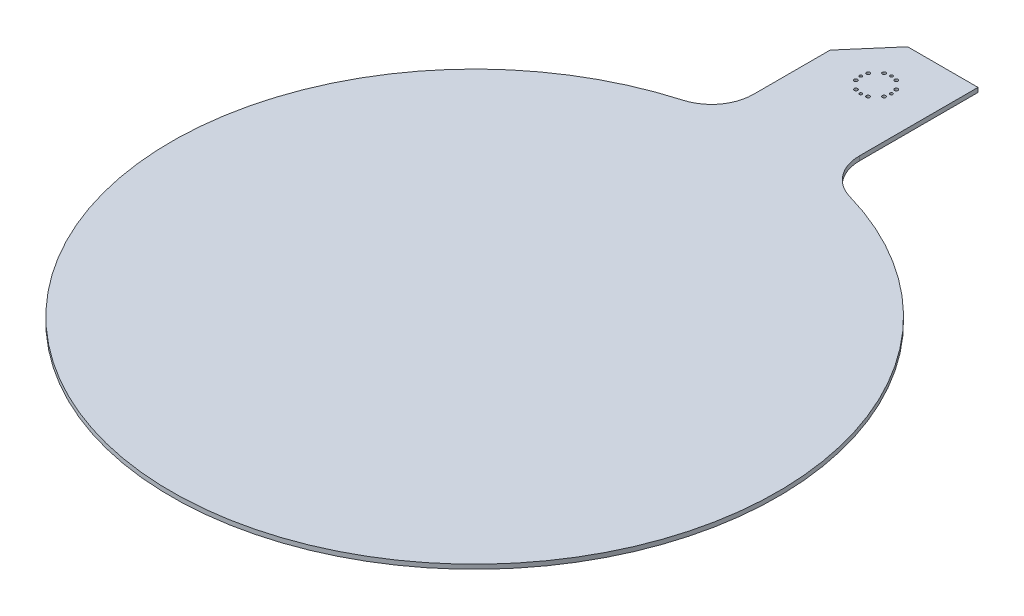
SolidWorks part; units mm, degrees
material "Oak"
ref_plane "Front Plane" through (0, 0, 0) normal (0, 0, 1) x (1, 0, 0)
ref_plane "Top Plane" through (0, 0, 0) normal (0, 1, 0) x (1, 0, 0)
ref_plane "Right Plane" through (0, 0, 0) normal (1, 0, 0) x (0, 0, -1)
sketch "Sketch1" plane through (-1.298, 0, -318.9577) normal (0, 1, 0) x (1, 0, 0)
  line L1 (-41.9696, 375.1077) -> (34.2304, 375.1077)
  line L2 (-41.9696, 375.1077) -> (-41.9696, 270.1544)
  line L4 (34.2304, 375.1077) -> (34.2304, 270.1544)
  arc A0 (-63.715, 241.3123) -> (55.9759, 241.3123) centre (-3.8696, 32.2077) ccw
  arc A1 (-63.715, 241.3123) -> (-41.9696, 270.1544) centre (-71.9696, 270.1544) ccw
  arc A2 (34.2304, 270.1544) -> (55.9759, 241.3123) centre (64.2304, 270.1544) ccw
  point P1 (-3.8696, 343.3577)
  dimension "D1" = 435
  dimension "D5" = 60
  dimension "D6" = 60
  dimension "D2" = 76.2
  dimension "D3" = 38.1
  dimension "D4" = 31.75
  dimension "D7" = 38.1
extrude "Boss-Extrude1" add sketch "Sketch1" along normal blind 3.175
sketch "Sketch20" plane through (0, 3.175, 0) normal (0, 1, 0) x (1, 0, 0)
  line L0 (32.9325, 694.0653) -> (-43.2675, 694.0653) construction
  line L1 (-43.2675, 694.0653) -> (-43.2675, 589.112) construction
  line L2 (-5.1675, 639.0653) -> (-24.0502, 606.3596) construction
  line L3 (-5.1675, 639.0653) -> (16.0174, 602.3719) construction
  line L4 (-5.1675, 639.0653) -> (-5.1675, 583.5294) construction
  circle A0 centre (-15.2571, 634.6835) radius 1.25
  circle A1 centre (-16.1675, 639.0653) radius 1
  circle A2 centre (-15.2571, 643.4471) radius 1.25
  circle A3 centre (-5.1675, 628.0653) radius 1
  circle A4 centre (-9.5494, 628.9757) radius 1.25
  circle A5 centre (-0.7857, 628.9757) radius 1.25
  circle A6 centre (-9.5494, 649.1549) radius 1.25
  circle A7 centre (-5.1675, 650.0653) radius 1
  circle A8 centre (-0.7857, 649.1549) radius 1.25
  circle A9 centre (4.9221, 643.4471) radius 1.25
  circle A10 centre (5.8325, 639.0653) radius 1
  circle A11 centre (4.9221, 634.6835) radius 1.25
  point P6 (-5.1675, 639.0653)
  dimension "D5" = 2
  dimension "D6" = 2.5
  dimension "D7" = 2.5
  dimension "D1" = 55
  dimension "D2" = 38.1
  dimension "D3" = 30
  dimension "D4" = 11
  dimension "D9" = 11
  dimension "D10" = 11
  dimension "D8" = 30
  dimension "D11" = 4
extrude "Cut-Extrude1" cut sketch "Sketch20" against normal through all
sketch "Sketch21" plane through (0, 3.175, 0) normal (0, 1, 0) x (1, 0, 0)
  line L0 (-43.2675, 694.0653) -> (-43.2675, 589.112) construction
  line L1 (32.9325, 694.0653) -> (-43.2675, 694.0653)
  line L2 (32.9325, 694.0653) -> (32.9325, 674.0653)
  line L3 (32.9325, 674.0653) -> (-17.5159, 674.0653)
  line L4 (-43.2675, 694.0653) -> (-43.2675, 674.0653)
  line L5 (-17.5159, 674.0653) -> (-43.2675, 644.1435)
  line L6 (-43.2675, 644.1435) -> (-43.2675, 674.0653)
  dimension "D1" = 20
extrude "Cut-Extrude2" cut sketch "Sketch21" against normal through all
